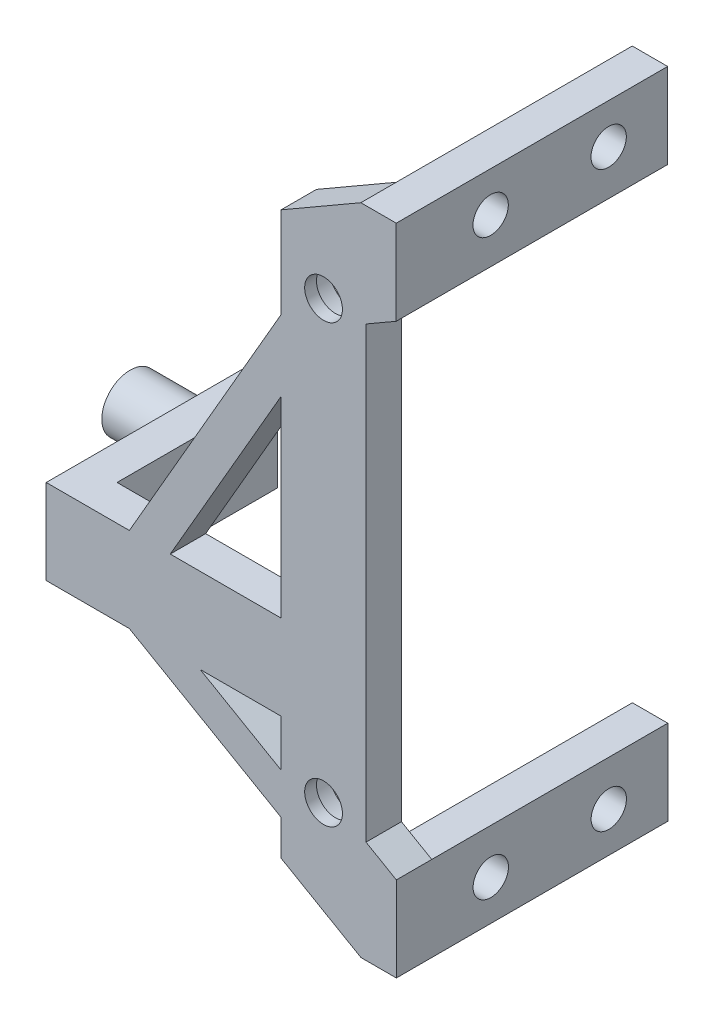
SolidWorks part; units mm, degrees
material "ABS"
ref_plane "Front Plane" through (0, 0, 0) normal (0, 0, 1) x (1, 0, 0)
ref_plane "Top Plane" through (0, 0, 0) normal (0, 1, 0) x (1, 0, 0)
ref_plane "Right Plane" through (0, 0, 0) normal (1, 0, 0) x (0, 0, -1)
sketch "Sketch1" plane through (0, 0, 0) normal (0, 0, 1) x (1, 0, 0)
  line L0 (0, 18.5) -> (0, -18.5) construction
  line L1 (0, 18.5) -> (0, 19.91) construction
  line L3 (-3.6, 23.2071) -> (-3.6, -24.3713) construction
  line L5 (3.6, 18.432) -> (3.6, -19.5962)
  line L6 (0, 19.91) -> (6.16, 19.91) construction
  line L7 (3.6, 18.432) -> (6.16, 19.91)
  line L8 (6.16, 19.91) -> (3.16, 27.11) construction
  line L9 (3.16, 27.11) -> (6.16, 27.11)
  line L10 (6.16, 27.11) -> (6.16, 19.91)
  line L11 (3.16, 27.11) -> (-3.6, 23.2071)
  line L12 (0, -18.5) -> (0, -21.08) construction
  line L13 (0, -21.08) -> (6.17, -21.08) construction
  line L14 (6.17, -21.08) -> (6.17, -28.28)
  line L15 (6.17, -28.28) -> (3.17, -28.28)
  line L16 (3.17, -28.28) -> (-3.6, -24.3713)
  line L17 (6.17, -21.08) -> (3.6, -19.5962)
  line L18 (0, -18.5) -> (0, -10.35) construction
  line L19 (0, -10.35) -> (-20.5, -10.35) construction
  line L20 (-20.5, -6.75) -> (-20.5, -13.95) construction
  line L21 (-20.5, -13.95) -> (-16.4541, -13.95)
  line L22 (-16.4541, -13.95) -> (-3.6, -21.3713)
  line L23 (-3.6, -21.3713) -> (-3.6, -24.3713)
  line L24 (-20.5, -6.75) -> (-16.4541, -6.75)
  line L25 (-16.4541, -6.75) -> (-3.6, 15.514)
  line L26 (-3.6, 15.514) -> (-3.6, 23.2071)
  line L27 (-16.4541, -13.95) -> (-16.4541, -6.75) construction
  line L28 (-16.4541, -13.95) -> (-3.6, -13.95) construction
  line L29 (-16.4541, -6.75) -> (-3.6, -6.75) construction
  line L30 (-10.4541, -13.95) -> (-3.6, -13.95)
  line L31 (-3.6, -13.95) -> (-3.6, -17.9072)
  line L32 (-3.6, -17.9072) -> (-10.4541, -13.95)
  line L33 (-20.5, -6.75) -> (-23.5, -6.75)
  line L34 (-23.5, -6.75) -> (-23.5, -13.95)
  line L35 (-23.5, -13.95) -> (-20.5, -13.95)
  line L36 (-3.6, -6.75) -> (-12.99, -6.75)
  line L37 (-12.99, -6.75) -> (-3.6, 9.514)
  line L38 (-3.6, 9.514) -> (-3.6, -6.75)
  circle A0 centre (0, 18.5) radius 1.6
  circle A1 centre (0, -18.5) radius 1.6
  point P4 (0, 0)
  point P23 (-20.5, -10.35)
  dimension "D2" = 3.2
  dimension "D3" = 3.2
  dimension "D1" = 37
  dimension "D7" = 1.41
  dimension "D8" = 6.16
  dimension "D4" = 30
  dimension "D5" = 7.2
  dimension "D6" = 3
  dimension "D9" = 7.2
  dimension "D10" = 2.58
  dimension "D11" = 6.17
  dimension "D12" = 7.2
  dimension "D13" = 3
  dimension "D14" = 30
  dimension "D15" = 8.15
  dimension "D16" = 20.5
  dimension "D17" = 7.2
  dimension "D18" = 30
  dimension "D19" = 60
  dimension "D20" = 3
  dimension "D21" = 3
  dimension "D22" = 3
  dimension "D23" = 3
extrude "Boss-Extrude1" add sketch "Sketch1" along normal blind 3
sketch "Sketch2" plane through (0, 0, 0) normal (0, 0, -1) x (-1, 0, 0)
  circle A0 centre (0, 18.5) radius 1.6 construction
  circle A1 centre (0, 18.5) radius 1.6 construction
  circle A2 centre (0, -18.5) radius 1.6 construction
  circle A3 centre (0, -18.5) radius 1.6 construction
  circle A4 centre (0, 18.5) radius 2.75
  circle A5 centre (0, -18.5) radius 2.75
  dimension "D1" = 5.5
extrude "Cut-Extrude1" cut sketch "Sketch2" against normal blind 2
sketch "Sketch4" plane through (0, 0, 0) normal (0, 0, -1) x (-1, 0, 0)
  line L1 (-3.16, 27.11) -> (-6.16, 27.11)
  line L2 (-3.16, 27.11) -> (-3.16, 19.91)
  line L3 (-3.16, 19.91) -> (-6.16, 19.91)
  line L4 (-6.16, 27.11) -> (-6.16, 19.91)
  line L5 (-3.17, -28.28) -> (-6.17, -28.28)
  line L6 (-3.17, -28.28) -> (-3.17, -21.08)
  line L7 (-3.17, -21.08) -> (-6.17, -21.08)
  line L8 (-6.17, -28.28) -> (-6.17, -21.08)
extrude "Boss-Extrude2" add sketch "Sketch4" along normal blind 20
sketch "Sketch5" plane through (3.16, 0, 0) normal (-1, 0, 0) x (0, 0, 1)
  line L0 (-10, 27.11) -> (-10, 19.91) construction
  line L1 (-20, 27.11) -> (0, 27.11) construction
  line L2 (-20, 19.91) -> (0, 19.91) construction
  line L3 (-5, 23.71) -> (-15, 23.71) construction
  line L4 (-10, -28.28) -> (-10, -21.08) construction
  line L5 (-20, -28.28) -> (0, -28.28) construction
  line L6 (-20, -21.08) -> (0, -21.08) construction
  line L7 (-15, -24.88) -> (-5, -24.88) construction
  circle A0 centre (-5, 23.71) radius 1.4975
  circle A1 centre (-15, 23.71) radius 1.4975
  circle A2 centre (-15, -24.88) radius 1.4975
  circle A3 centre (-5, -24.88) radius 1.4975
  point P11 (-10, 23.71)
  point P20 (-10, -24.88)
  dimension "D3" = 2.995
  dimension "D4" = 2.995
  dimension "D7" = 2.995
  dimension "D8" = 2.995
  dimension "D1" = 10
  dimension "D2" = 3.4
  dimension "D5" = 3.4
  dimension "D6" = 10
extrude "Cut-Extrude2" cut sketch "Sketch5" against normal up to next
sketch "Sketch7" plane through (-23.5, 0, 0) normal (-1, 0, 0) x (0, 0, 1)
  line L0 (0, -10.35) -> (-10, -10.35) construction
  line L1 (0, -6.75) -> (-13.6, -6.75)
  line L2 (0, -6.75) -> (0, -13.95)
  line L3 (0, -13.95) -> (-13.6, -13.95)
  line L4 (-13.6, -6.75) -> (-13.6, -13.95)
  line L5 (-10, -10.35) -> (-10, -6.75) construction
  line L6 (0, -6.75) -> (0, -13.95) construction
  line L7 (-10, -10.35) -> (-13.6, -10.35) construction
  circle A0 centre (-10, -10.35) radius 2.35 construction
  dimension "D1" = 10
  dimension "D2" = 4.7
extrude "Boss-Extrude3" add sketch "Sketch7" against normal blind 3
sketch "Sketch8" plane through (-23.5, 0, 0) normal (-1, 0, 0) x (0, 0, 1)
  line L0 (-13.6, -10.35) -> (-13.6, -13.95) construction
  line L1 (-13.6, -6.75) -> (-10, -6.75) construction
  line L2 (-13.6, -6.75) -> (-13.6, -10.35) construction
  line L3 (-13.6, -10.35) -> (-10, -10.35) construction
  line L4 (-10, -6.75) -> (-10, -10.35) construction
  circle A0 centre (-10, -10.35) radius 2.4
  dimension "D1" = 4.8
extrude "Boss-Extrude4" add sketch "Sketch8" along normal blind 5.89
equation "\"reg-tolerance\"= .2mm"
equation "\"tight-tolerance\"= .15mm"
equation "\"loose-tolerance\"= .3mm"
equation "\"thiccness\"= 3mm"
equation "\"D3@Sketch1\"=\"D2@Sketch1\""
equation "\"D1@Boss-Extrude1\"=\"thiccness\""
equation "\"D6@Sketch1\"=\"thiccness\""
equation "\"D9@Sketch1\"=\"D5@Sketch1\""
equation "\"D7@Sketch1\"=\"reg-tolerance\"+1.21"
equation "\"D5@Sketch1\"=7.40mm-\"reg-tolerance\""
equation "\"6.36mm-\"=6.36"
equation "\"D8@Sketch1\"=6.36-\"reg-tolerance\""
equation "\"D10@Sketch1\"=2.38+\"reg-tolerance\""
equation "\"D11@Sketch1\"=6.37-\"reg-tolerance\""
equation "\"D12@Sketch1\"=\"D5@Sketch1\""
equation "\"D13@Sketch1\"=\"D6@Sketch1\""
equation "\"D14@Sketch1\"=\"D4@Sketch1\""
equation "\"D3@Sketch5\"=\"tight-tolerance\"+2.845"
equation "\"D4@Sketch5\"=\"D3@Sketch5\""
equation "\"D7@Sketch5\"=\"D4@Sketch5\""
equation "\"D8@Sketch5\"=\"D7@Sketch5\""
equation "\"D17@Sketch1\"=\"D9@Sketch1\""
equation "\"D20@Sketch1\"=\"thiccness\""
equation "\"D21@Sketch1\"=\"thiccness\""
equation "\"D22@Sketch1\"=\"thiccness\""
equation "\"D23@Sketch1\"=\"thiccness\""
equation "\"D2@Sketch7\"=5-\"loose-tolerance\""
equation "\"D1@Boss-Extrude3\"=\"thiccness\""
equation "\"D1@Sketch8\"=5-\"reg-tolerance\""
